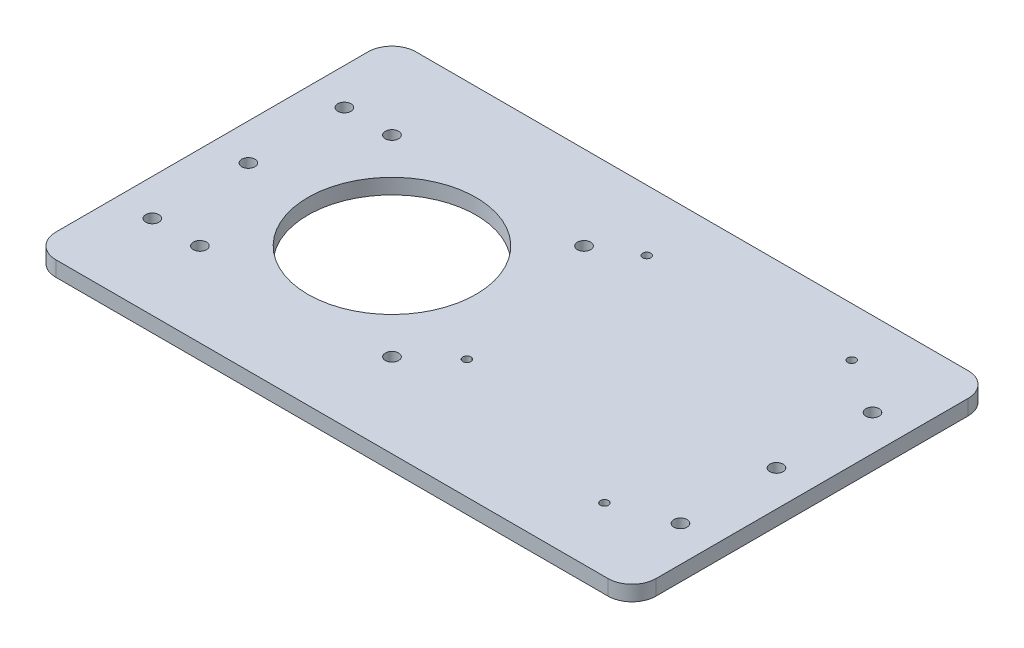
SolidWorks part; units mm, degrees
ref_plane "Front Plane" through (0, 0, 0) normal (0, 0, 1) x (1, 0, 0)
ref_plane "Top Plane" through (0, 0, 0) normal (0, 1, 0) x (1, 0, 0)
ref_plane "Right Plane" through (0, 0, 0) normal (1, 0, 0) x (0, 0, -1)
sketch "Sketch1" plane through (0, 0, 0) normal (0, 1, 0) x (1, 0, 0)
  line L0 (0, 75.1782) -> (0, -76.1513) construction
  line L1 (-89.046, 0) -> (105.59, 0) construction
  line L3 (175, -75) -> (-75, -75)
  line L4 (175, -75) -> (175, 75)
  line L5 (175, 75) -> (-75, 75)
  line L6 (-75, -75) -> (-75, 75)
  point P4 (0, 0)
  dimension "D1" = 250
  dimension "D2" = 150
  dimension "D3" = 75
  dimension "D4" = 75
extrude "Boss-Extrude1" add sketch "Sketch1" along normal blind 6.35
sketch "Sketch2" plane through (0, 6.35, 0) normal (0, 1, 0) x (1, 0, 0)
  line L0 (0, 118.2487) -> (0, -103.3269) construction
  line L1 (-114.109, 0) -> (130.6821, 0) construction
  circle A0 centre (0, 0) radius 35
  circle A1 centre (-40, 40) radius 2.75
  circle A2 centre (40, 40) radius 2.75
  circle A3 centre (-40, -40) radius 2.75
  circle A4 centre (40, -40) radius 2.75
  dimension "D1" = 70
  dimension "D2" = 5.5
  dimension "D3" = 40
  dimension "D4" = 40
extrude "Cut-Extrude1" cut sketch "Sketch2" against normal through all
fillet "Fillet1" radius 10 4 edges at (-75, 3.175, -75) (175, 3.175, -75) (-75, 3.175, 75) (175, 3.175, 75)
hole_wizard "CSK for M5 Flat Head Machine Screw1" positions "Sketch5" profile "Sketch3" countersink size "M5" standard "ANSI Metric" end condition through all
sketch "Sketch5" plane through (0, 0, 0) normal (0, -1, 0) x (-1, 0, 0)
  line L0 (59.8283, 40) -> (-160.1717, 40) construction
  line L1 (-160.1717, 40) -> (-160.1717, 0) construction
  line L2 (-160.1717, 0) -> (-160.1717, -40) construction
  line L3 (-160.1717, -40) -> (59.8283, -40) construction
  line L4 (59.8283, -40) -> (59.8283, 0) construction
  line L5 (59.8283, 0) -> (59.8283, 40) construction
  line L6 (0, 0) -> (-160.1717, 0) construction
  line L8 (0, 0) -> (59.8283, 0) construction
  line L9 (-50.1717, -40) -> (-50.1717, 40) construction
  point P0 (59.8283, 40)
  point P2 (59.8283, 0)
  point P4 (59.8283, -40)
  point P6 (-160.1717, 40)
  point P8 (-160.1717, 0)
  point P10 (-160.1717, -40)
  dimension "D1" = 40
  dimension "D2" = 40
  dimension "D3" = 220
  dimension "D4" = 110
sketch "Sketch3" plane through (-59.8283, 0, -40) normal (1, 0, 0) x (0, 0, -1)
  line L0 (0, 0) -> (0, 6.35)
  line L1 (0, 6.35) -> (2.75, 6.35)
  line L2 (2.75, 6.35) -> (2.75, 2.45)
  line L3 (2.75, 2.45) -> (5.2, 0)
  line L5 (5.2, 0) -> (0, 0)
  line L6 (-2.75, 2.45) -> (-5.2, 0) construction
  line L11 (0, -6.35) -> (0, 107.95) construction
  dimension "Thru Hole Dia." = 5.5
  dimension "Thru Hole Depth" = 6.35
  dimension "Near C'Sink Dia." = 10.4
  dimension "Near C'Sink Angle" = 90
hole_wizard "CSK for M3 Flat Head Machine Screw1" positions "Sketch7" profile "Sketch6" countersink size "M3" standard "ANSI Metric" end condition through all
sketch "Sketch7" plane through (0, 0, 0) normal (0, -1, 0) x (-1, 0, 0)
  line L0 (-136.9647, -48.4522) -> (-136.9647, 54.5478) construction
  line L1 (-136.9647, 54.5478) -> (-56.5047, 54.5478) construction
  line L2 (-56.5047, 54.5478) -> (-56.5047, -48.4522) construction
  line L3 (-56.5047, -48.4522) -> (-136.9647, -48.4522) construction
  point P0 (-136.9647, -48.4522)
  point P2 (-56.5047, -25.2867)
  point P4 (-56.5047, 49.6133)
  point P6 (-136.9647, 54.5478)
  dimension "D1" = 103
  dimension "D2" = 74.9
  dimension "D3" = 80.46
sketch "Sketch6" plane through (136.9647, 0, 48.4522) normal (1, 0, 0) x (0, 0, -1)
  line L0 (0, 0) -> (0, 6.35)
  line L1 (0, 6.35) -> (1.7, 6.35)
  line L2 (1.7, 6.35) -> (1.7, 1.45)
  line L3 (1.7, 1.45) -> (3.15, 0)
  line L5 (3.15, 0) -> (0, 0)
  line L6 (-1.7, 1.45) -> (-3.15, 0) construction
  line L11 (0, -6.35) -> (0, 107.95) construction
  dimension "Thru Hole Dia." = 3.4
  dimension "Thru Hole Depth" = 6.35
  dimension "Near C'Sink Dia." = 6.3
  dimension "Near C'Sink Angle" = 90
equation "\"connector_D1\" = 70 'the big holes diameter"
equation "\"mtg_hole_D\" = 5.5 'mounting holes"
equation "\"mtg_dfc\" = 40 'mounting hole distance from center"
equation "\"plate_thickness\" = 6.35 'thickness of the plate "
equation "\"t_height\" = 200"
equation "\"t_width\" = 240"
equation "\"t_length\" = 240"
equation "\"plate_hole_from_edge\" = 9"
equation "\"plate_spacing\" = 1"
equation "\"front_plate_height\" = \"t_height\" + 38"
equation "\"front_plate_width\" = \"t_width\" + 38"
equation "\"side_plate_height\" = \"front_plate_height\""
equation "\"side_plate_length\" = \"t_length\" + 38"
equation "\"top_plate_width\" = \"front_plate_width\""
equation "\"top_plate_length\" = \"side_plate_length\""
equation "\"itx_support_t_slot_length\" = \"t_width\" + (2 * 20.5)"
equation "\"locomotion_length\" = \"t_length\""
equation "\"locomotion_width\" = \"t_width\""
equation "\"locomotion_height\" = 40"
equation "\"itx_mtg_hole_spacing\" = 40"
equation "\"D1@Sketch2\"=\"connector_D1\""
equation "\"D2@Sketch2\"=\"mtg_hole_D\""
equation "\"D3@Sketch2\"=\"mtg_dfc\""
equation "\"D4@Sketch2\"=\"mtg_dfc\""
equation "\"D1@Boss-Extrude1\"=\"plate_thickness\""
equation "\"D4@Sketch1\"=\"D2@Sketch1\"/2"
equation "\"D2@Sketch5\"=\"mtg_dfc\""
equation "\"D1@Sketch5\"=\"mtg_dfc\""
